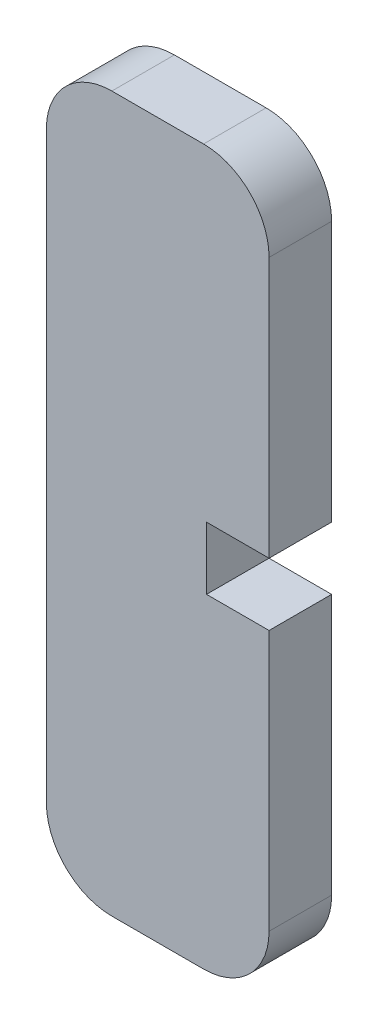
SolidWorks part; units mm, degrees
ref_plane "Front Plane" through (0, 0, 0) normal (0, 0, 1) x (1, 0, 0)
ref_plane "Top Plane" through (0, 0, 0) normal (0, 1, 0) x (1, 0, 0)
ref_plane "Right Plane" through (0, 0, 0) normal (1, 0, 0) x (0, 0, -1)
sketch "Sketch1" plane through (0, 0, 0) normal (0, 0, 1) x (1, 0, 0)
  line L0 (0.2248, 49.7752) -> (7.2248, 49.7752) construction
  line L1 (0.2248, -4.7752) -> (7.2248, -4.7752) construction
  line L2 (0.2248, 49.7752) -> (7.2248, 49.7752) construction
  line L3 (0.2248, -4.7752) -> (7.2248, -4.7752) construction
  line L4 (0.2248, 49.7752) -> (-4.5504, 49.7752) construction
  line L5 (0.2248, -4.7752) -> (-4.5504, -4.7752) construction
  line L6 (-4.5504, 44.7752) -> (-4.5504, 0.2248)
  line L7 (0.4496, -4.7752) -> (7.4496, -4.7752)
  line L8 (0.4496, 49.7752) -> (7.4496, 49.7752)
  line L9 (12.4496, 44.7752) -> (12.4496, 0.2248)
  arc A0 (-4.5504, 44.7752) -> (0.4496, 49.7752) centre (0.4496, 44.7752) cw
  arc A1 (-4.5504, 0.2248) -> (0.4496, -4.7752) centre (0.4496, 0.2248) ccw
  arc A2 (7.4496, -4.7752) -> (12.4496, 0.2248) centre (7.4496, 0.2248) ccw
  arc A3 (7.4496, 49.7752) -> (12.4496, 44.7752) centre (7.4496, 44.7752) cw
  point P16 (12.4496, -4.7752)
  point P19 (12.4496, 49.7752)
  dimension "D5" = 5
  dimension "D1" = 4.7752
  dimension "D2" = 4.7752
  dimension "D3" = 17
  dimension "D4" = 17
extrude "Boss-Extrude1" add sketch "Sketch1" along normal blind 4.7752
sketch "Sketch2" plane through (0, 0, 0) normal (0, 0, -1) x (-1, 0, 0)
  line L0 (-12.4496, 0.2248) -> (-12.4496, 22.5) construction
  line L1 (-12.4496, 0.2248) -> (-12.4496, 44.7752) construction
  line L2 (-12.4496, 22.5) -> (-7.6744, 22.5) construction
  line L3 (-7.6744, 20.1124) -> (-7.6744, 24.8876)
  line L4 (-7.6744, 24.8876) -> (-12.4496, 24.8876)
  line L5 (-7.6744, 20.1124) -> (-12.4496, 20.1124)
  line L6 (-12.4496, 20.1124) -> (-12.4496, 24.8876)
  dimension "D1" = 4.7752
  dimension "D2" = 2.3876
extrude "Cut-Extrude1" cut sketch "Sketch2" against normal blind 4.7752
